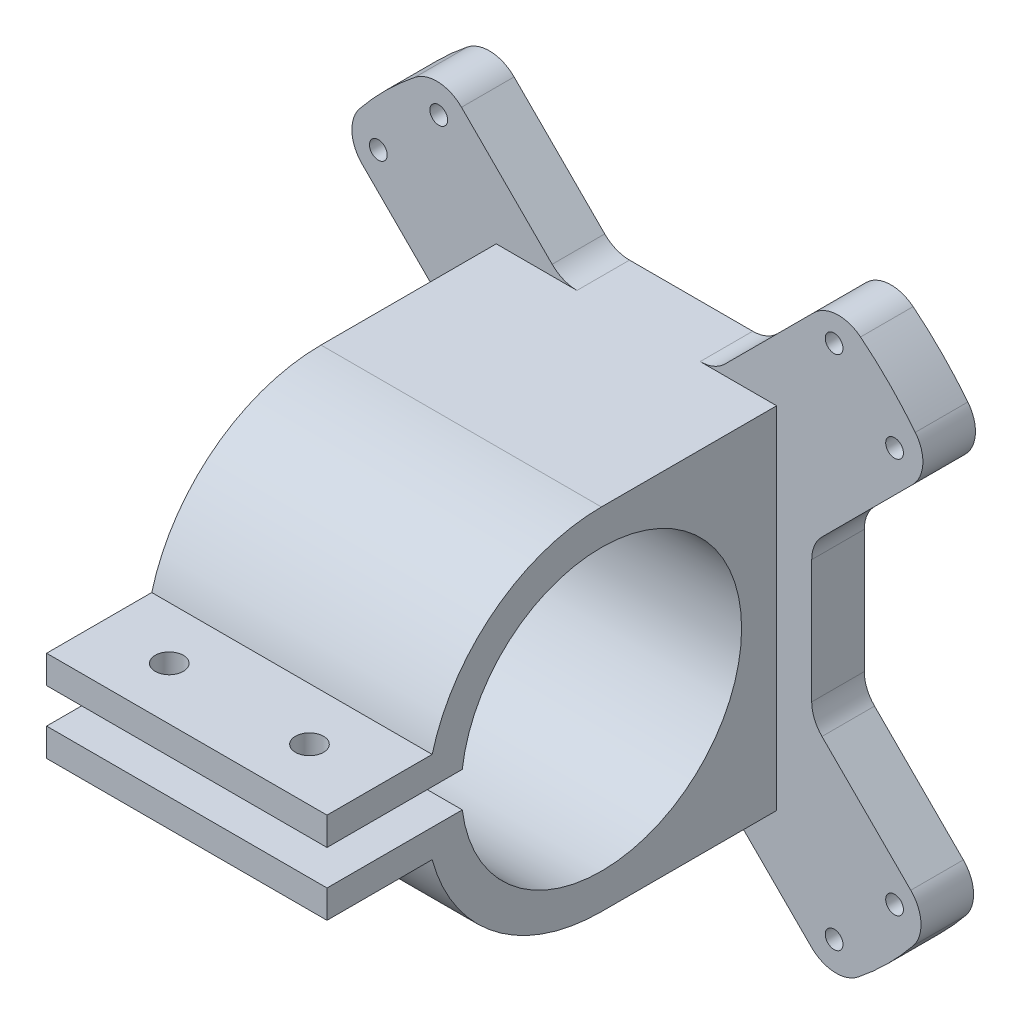
SolidWorks part; units mm, degrees
material "ABS"
ref_plane "Front Plane" through (0, 0, 0) normal (0, 0, 1) x (1, 0, 0)
ref_plane "Top Plane" through (0, 0, 0) normal (0, 1, 0) x (1, 0, 0)
ref_plane "Right Plane" through (0, 0, 0) normal (1, 0, 0) x (0, 0, -1)
sketch "Model" plane through (0, 0, 0) normal (0, 0, 1) x (1, 0, 0)
  line L0 (-68.7229, -13.335) -> (-68.7229, -12.065)
  line L1 (-67.4529, -10.795) -> (-44.5929, -10.795)
  line L2 (-43.3229, -12.065) -> (-43.3229, -13.335)
  line L3 (-44.5929, -14.605) -> (-67.4529, -14.605)
  line L4 (-43.3229, 13.335) -> (-43.3229, 12.065)
  line L5 (-44.5929, 10.795) -> (-67.4529, 10.795)
  line L6 (-68.7229, 12.065) -> (-68.7229, 13.335)
  line L7 (-67.4529, 14.605) -> (-44.5929, 14.605)
  line L8 (67.4529, 10.795) -> (44.5929, 10.795)
  line L9 (43.3229, 12.065) -> (43.3229, 13.335)
  line L10 (44.5929, 14.605) -> (67.4529, 14.605)
  line L11 (68.7229, 13.335) -> (68.7229, 12.065)
  line L12 (44.5929, -10.795) -> (67.4529, -10.795)
  line L13 (68.7229, -12.065) -> (68.7229, -13.335)
  line L14 (67.4529, -14.605) -> (44.5929, -14.605)
  line L15 (43.3229, -13.335) -> (43.3229, -12.065)
  line L16 (1.27, -16.51) -> (1.27, -39.37)
  line L17 (-1.27, -39.37) -> (-1.27, -16.51)
  line L18 (-10.7763, -12.5724) -> (-26.9408, -28.7368)
  line L19 (-28.7368, -26.9408) -> (-12.5724, -10.7763)
  line L20 (-16.51, -1.27) -> (-39.37, -1.27)
  line L21 (-39.37, 1.27) -> (-16.51, 1.27)
  line L22 (-12.5724, 10.7763) -> (-28.7368, 26.9408)
  line L23 (-26.9408, 28.7368) -> (-10.7763, 12.5724)
  line L24 (-1.27, 16.51) -> (-1.27, 39.37)
  line L25 (1.27, 39.37) -> (1.27, 16.51)
  line L26 (10.7763, 12.5724) -> (26.9408, 28.7368)
  line L27 (28.7368, 26.9408) -> (12.5724, 10.7763)
  line L28 (16.51, 1.27) -> (39.37, 1.27)
  line L29 (39.37, -1.27) -> (16.51, -1.27)
  line L30 (12.5724, -10.7763) -> (28.7368, -26.9408)
  line L31 (26.9408, -28.7368) -> (10.7763, -12.5724)
  line L32 (-23.2448, 44.45) -> (23.2448, 44.45)
  line L33 (-71.5169, 23.8125) -> (-47.8309, 23.8125)
  line L34 (-76.5969, 18.7325) -> (-71.5169, 23.8125)
  line L35 (-76.5969, -18.7325) -> (-76.5969, 18.7325)
  line L36 (-71.5169, -23.8125) -> (-76.5969, -18.7325)
  line L37 (-47.8309, -23.8125) -> (-71.5169, -23.8125)
  line L38 (23.2448, -44.45) -> (-23.2448, -44.45)
  line L39 (71.5169, -23.8125) -> (47.8309, -23.8125)
  line L40 (76.5969, -18.7325) -> (71.5169, -23.8125)
  line L41 (76.5969, 18.7325) -> (76.5969, -18.7325)
  line L42 (71.5169, 23.8125) -> (76.5969, 18.7325)
  line L43 (47.8309, 23.8125) -> (71.5169, 23.8125)
  arc A0 (-68.7229, -13.335) -> (-67.4529, -14.605) centre (-67.4529, -13.335) ccw
  arc A1 (-67.4529, -10.795) -> (-68.7229, -12.065) centre (-67.4529, -12.065) ccw
  arc A2 (-43.3229, -12.065) -> (-44.5929, -10.795) centre (-44.5929, -12.065) ccw
  arc A3 (-44.5929, -14.605) -> (-43.3229, -13.335) centre (-44.5929, -13.335) ccw
  arc A4 (-43.3229, 13.335) -> (-44.5929, 14.605) centre (-44.5929, 13.335) ccw
  arc A5 (-44.5929, 10.795) -> (-43.3229, 12.065) centre (-44.5929, 12.065) ccw
  arc A6 (-68.7229, 12.065) -> (-67.4529, 10.795) centre (-67.4529, 12.065) ccw
  arc A7 (-67.4529, 14.605) -> (-68.7229, 13.335) centre (-67.4529, 13.335) ccw
  arc A8 (67.4529, 10.795) -> (68.7229, 12.065) centre (67.4529, 12.065) ccw
  arc A9 (43.3229, 12.065) -> (44.5929, 10.795) centre (44.5929, 12.065) ccw
  arc A10 (44.5929, 14.605) -> (43.3229, 13.335) centre (44.5929, 13.335) ccw
  arc A11 (68.7229, 13.335) -> (67.4529, 14.605) centre (67.4529, 13.335) ccw
  arc A12 (44.5929, -10.795) -> (43.3229, -12.065) centre (44.5929, -12.065) ccw
  arc A13 (68.7229, -12.065) -> (67.4529, -10.795) centre (67.4529, -12.065) ccw
  arc A14 (67.4529, -14.605) -> (68.7229, -13.335) centre (67.4529, -13.335) ccw
  arc A15 (43.3229, -13.335) -> (44.5929, -14.605) centre (44.5929, -13.335) ccw
  arc A16 (1.27, -16.51) -> (-1.27, -16.51) centre (0, -16.51) ccw
  arc A17 (-1.27, -39.37) -> (1.27, -39.37) centre (0, -39.37) ccw
  arc A18 (-10.7763, -12.5724) -> (-12.5724, -10.7763) centre (-11.6743, -11.6743) ccw
  arc A19 (-28.7368, -26.9408) -> (-26.9408, -28.7368) centre (-27.8388, -27.8388) ccw
  arc A20 (-16.51, -1.27) -> (-16.51, 1.27) centre (-16.51, 0) ccw
  arc A21 (-39.37, 1.27) -> (-39.37, -1.27) centre (-39.37, 0) ccw
  arc A22 (-12.5724, 10.7763) -> (-10.7763, 12.5724) centre (-11.6743, 11.6743) ccw
  arc A23 (-26.9408, 28.7368) -> (-28.7368, 26.9408) centre (-27.8388, 27.8388) ccw
  arc A24 (-1.27, 16.51) -> (1.27, 16.51) centre (0, 16.51) ccw
  arc A25 (1.27, 39.37) -> (-1.27, 39.37) centre (0, 39.37) ccw
  arc A26 (10.7763, 12.5724) -> (12.5724, 10.7763) centre (11.6743, 11.6743) ccw
  arc A27 (28.7368, 26.9408) -> (26.9408, 28.7368) centre (27.8388, 27.8388) ccw
  arc A28 (16.51, 1.27) -> (16.51, -1.27) centre (16.51, 0) ccw
  arc A29 (39.37, -1.27) -> (39.37, 1.27) centre (39.37, 0) ccw
  arc A30 (12.5724, -10.7763) -> (10.7763, -12.5724) centre (11.6743, -11.6743) ccw
  arc A31 (26.9408, -28.7368) -> (28.7368, -26.9408) centre (27.8388, -27.8388) ccw
  circle A32 centre (-36.8191, -28.198) radius 1.016
  circle A33 centre (-36.8191, 28.198) radius 1.016
  circle A34 centre (36.8191, 28.198) radius 1.016
  circle A35 centre (0, 0) radius 6.35
  arc A36 (25.8276, 43.7444) -> (23.2448, 44.45) centre (23.2448, 39.37) ccw
  arc A37 (-23.2448, 44.45) -> (-25.8276, 43.7444) centre (-23.2448, 39.37) ccw
  arc A38 (-25.8276, 43.7444) -> (-43.4827, 26.2659) centre (0, 0) ccw
  arc A39 (-47.8309, 23.8125) -> (-43.4827, 26.2659) centre (-47.8309, 28.8925) ccw
  arc A40 (-43.4827, -26.2659) -> (-47.8309, -23.8125) centre (-47.8309, -28.8925) ccw
  arc A41 (-43.4827, -26.2659) -> (-25.8276, -43.7444) centre (0, 0) ccw
  arc A42 (-25.8276, -43.7444) -> (-23.2448, -44.45) centre (-23.2448, -39.37) ccw
  arc A43 (23.2448, -44.45) -> (25.8276, -43.7444) centre (23.2448, -39.37) ccw
  arc A44 (25.8276, -43.7444) -> (43.4827, -26.2659) centre (0, 0) ccw
  arc A45 (47.8309, -23.8125) -> (43.4827, -26.2659) centre (47.8309, -28.8925) ccw
  arc A46 (43.4827, 26.2659) -> (47.8309, 23.8125) centre (47.8309, 28.8925) ccw
  arc A47 (43.4827, 26.2659) -> (25.8276, 43.7444) centre (0, 0) ccw
  circle A48 centre (36.8191, -28.198) radius 1.016
  circle A49 centre (28.198, -36.8191) radius 1.016
  circle A50 centre (28.198, 36.8191) radius 1.016
  circle A51 centre (-28.198, 36.8191) radius 1.016
  circle A52 centre (-28.198, -36.8191) radius 1.016
sketch "Sketch2" plane through (0, 0, 0) normal (0, 0, 1) x (1, 0, 0)
  line L0 (-27.8388, 27.8388) -> (-11.6743, 11.6743) construction
  line L1 (27.8388, 27.8388) -> (11.6743, 11.6743) construction
  line L3 (39.37, 0) -> (16.51, 0) construction
  line L5 (27.8388, -27.8388) -> (11.6743, -11.6743) construction
  line L7 (0, -39.37) -> (0, -16.51) construction
  line L9 (-27.8388, -27.8388) -> (-11.6743, -11.6743) construction
  line L11 (-39.37, 0) -> (-16.51, 0) construction
  line L14 (0, 16.51) -> (0, 39.37) construction
sketch "Sketch8" plane through (0, 0, 0) normal (0, 0, 1) x (1, 0, 0)
  line L1 (-26.4645, 12.6211) -> (-39.1297, 25.2863)
  line L2 (8.488, -25) -> (-9.0856, -25)
  line L3 (25, -9.0856) -> (25, 8.488)
  line L4 (9.0856, 25) -> (-8.488, 25)
  line L5 (-25, -8.488) -> (-25, 9.0856)
  line L6 (-27.8388, 27.8388) -> (-11.6743, 11.6743) construction
  line L7 (25, -25) -> (-25, -25) construction
  line L8 (-12.6211, -26.4645) -> (-25.2863, -39.1297)
  line L9 (-39.3956, -24.9547) -> (-26.4645, -12.0236)
  line L10 (-24.9547, 39.3956) -> (-12.0236, 26.4645)
  line L11 (12.6211, 26.4645) -> (25.2863, 39.1297)
  line L12 (39.3956, 24.9547) -> (26.4645, 12.0236)
  line L13 (26.4645, -12.6211) -> (39.1297, -25.2863)
  line L14 (24.9547, -39.3956) -> (12.0236, -26.4645)
  line L15 (25, -25) -> (25, 25) construction
  line L16 (25, 25) -> (-25, 25) construction
  line L17 (-25, -25) -> (-25, 25) construction
  line L18 (25, -25) -> (-25, 25) construction
  line L19 (25, 25) -> (-25, -25) construction
  arc A8 (-39.7749, -31.6005) -> (-31.9683, -39.48) centre (0, 0) ccw
  circle A9 centre (-28.198, -36.8191) radius 1.266
  arc A10 (-39.3956, -24.9547) -> (-39.7749, -31.6005) centre (-35.8601, -28.4902) ccw
  circle A29 centre (-36.8191, -28.198) radius 1.266
  circle A30 centre (-36.8191, 28.198) radius 1.266
  circle A31 centre (-28.198, 36.8191) radius 1.266
  circle A32 centre (28.198, 36.8191) radius 1.266
  circle A33 centre (36.8191, 28.198) radius 1.266
  circle A34 centre (36.8191, -28.198) radius 1.266
  circle A35 centre (28.198, -36.8191) radius 1.266
  circle A36 centre (-28.198, -36.8191) radius 1.016 construction
  arc A37 (-43.4827, -26.2659) -> (-25.8276, -43.7444) centre (0, 0) ccw construction
  arc A38 (-25.2863, -39.1297) -> (-31.9683, -39.48) centre (-28.8218, -35.5941) cw
  arc A39 (-26.4645, -12.0236) -> (-25, -8.488) centre (-30, -8.488) ccw
  arc A40 (-12.6211, -26.4645) -> (-9.0856, -25) centre (-9.0856, -30) cw
  arc A41 (-39.1297, 25.2863) -> (-39.48, 31.9683) centre (-35.5941, 28.8218) cw
  arc A42 (-31.6005, 39.7749) -> (-39.48, 31.9683) centre (0, 0) ccw
  arc A43 (-24.9547, 39.3956) -> (-31.6005, 39.7749) centre (-28.4902, 35.8601) ccw
  arc A44 (-12.0236, 26.4645) -> (-8.488, 25) centre (-8.488, 30) ccw
  arc A45 (-26.4645, 12.6211) -> (-25, 9.0856) centre (-30, 9.0856) cw
  arc A46 (25.2863, 39.1297) -> (31.9683, 39.48) centre (28.8218, 35.5941) cw
  arc A47 (39.7749, 31.6005) -> (31.9683, 39.48) centre (0, 0) ccw
  arc A48 (39.3956, 24.9547) -> (39.7749, 31.6005) centre (35.8601, 28.4902) ccw
  arc A49 (26.4645, 12.0236) -> (25, 8.488) centre (30, 8.488) ccw
  arc A50 (12.6211, 26.4645) -> (9.0856, 25) centre (9.0856, 30) cw
  arc A51 (39.1297, -25.2863) -> (39.48, -31.9683) centre (35.5941, -28.8218) cw
  arc A52 (31.6005, -39.7749) -> (39.48, -31.9683) centre (0, 0) ccw
  arc A53 (24.9547, -39.3956) -> (31.6005, -39.7749) centre (28.4902, -35.8601) ccw
  arc A54 (12.0236, -26.4645) -> (8.488, -25) centre (8.488, -30) ccw
  arc A55 (26.4645, -12.6211) -> (25, -9.0856) centre (30, -9.0856) cw
  point P0 (0, 0)
  point P11 (-42.4083, -27.9674)
  dimension "D1" = 50
  dimension "D2" = 0.25
  dimension "D5" = 5
  dimension "D6" = 5
  dimension "D4" = 4
  dimension "D3" = 20
extrude "Boss-Extrude3" add sketch "Sketch8" along normal blind 7.5
sketch "Sketch9" plane through (0, 0, 0) normal (1, 0, 0) x (0, 0, -1)
  line L0 (-7.5, -25) -> (-7.5, 25)
  line L3 (-7.5, -25) -> (0, 0) construction
  line L4 (0, 6.35) -> (0, -6.35) construction
  line L5 (0, 0) -> (-7.5, 25) construction
  line L6 (-7.5, -8.488) -> (-7.5, 9.0856) construction
  line L7 (-7.5, -25) -> (-32.5, -25)
  line L8 (-7.5, 25) -> (-32.5, 25)
  line L9 (-52.3431, -2.5) -> (-71.6402, -2.5)
  line L10 (-56.6402, -6.5) -> (-71.6402, -6.5)
  line L11 (-71.6402, 2.5) -> (-52.3431, 2.5)
  line L12 (-71.6402, -6.5) -> (-71.6402, -2.5)
  line L13 (-71.6402, 2.5) -> (-71.6402, 6.5)
  line L14 (-71.6402, 6.5) -> (-56.6402, 6.5)
  arc A0 (-32.5, -25) -> (-56.6402, -6.5) centre (-32.5, 0) cw
  arc A1 (-52.3431, -2.5) -> (-52.3431, 2.5) centre (-32.5, 0) ccw
  arc A3 (-56.6402, 6.5) -> (-32.5, 25) centre (-32.5, 0) cw
  dimension "D3" = 5
  dimension "D6" = 25
  dimension "D1" = 50
  dimension "D2" = 25
  dimension "D4" = 4
  dimension "D5" = 5
  dimension "D7" = 15
extrude "Boss-Extrude4" add sketch "Sketch9" along normal mid plane 40
sketch "Sketch10" plane through (0, 6.5, 0) normal (0, 1, 0) x (1, 0, 0)
  line L2 (-10, -64.1402) -> (0, 0) construction
  line L3 (0, 0) -> (10, -64.1402) construction
  line L4 (20, -56.6402) -> (-20, -56.6402) construction
  circle A0 centre (-10, -64.1402) radius 2
  circle A1 centre (10, -64.1402) radius 2
  dimension "D2" = 4
  dimension "D3" = 20
  dimension "D1" = 7.5
extrude "Cut-Extrude3" cut sketch "Sketch10" against normal up to surface (13 mm away) up to face at (0, -6.5, 64.1402)
